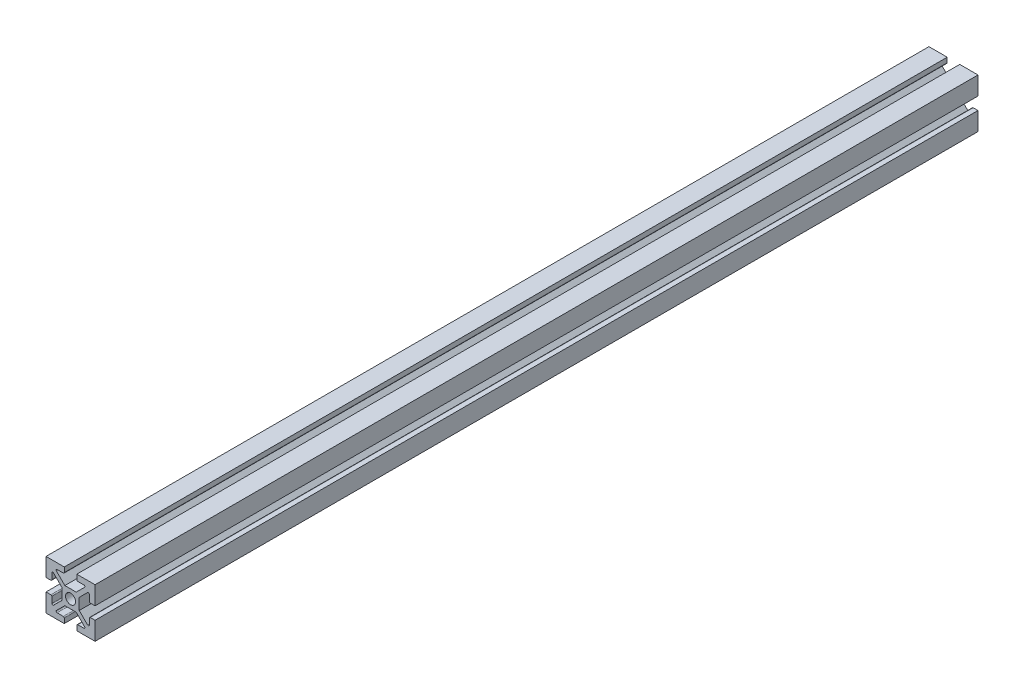
SolidWorks part; units mm, degrees
ref_plane "Front Plane" through (0, 0, 0) normal (0, 0, 1) x (1, 0, 0)
ref_plane "Top Plane" through (0, 0, 0) normal (0, 1, 0) x (1, 0, 0)
ref_plane "Right Plane" through (0, 0, 0) normal (1, 0, 0) x (0, 0, -1)
sketch "Sketch2" plane through (0, 0, 0) normal (0, 0, 1) x (1, 0, 0)
  line L1 (-12.7, -12.7) -> (12.7, -12.7)
  line L2 (-12.7, -12.7) -> (-12.7, 12.7)
  line L3 (-12.7, 12.7) -> (12.7, 12.7)
  line L4 (12.7, -12.7) -> (12.7, 12.7)
  line L5 (-12.7, -12.7) -> (12.7, 12.7) construction
  line L6 (-12.7, 12.7) -> (12.7, -12.7) construction
  point P0 (0, 0)
  dimension "D1" = 25.4
  dimension "D2" = 25.4
extrude "Boss-Extrude2" add sketch "Sketch2" along normal blind 457.2
sketch "Sketch3" plane through (0, 0, 457.2) normal (0, 0, 1) x (1, 0, 0)
  line L0 (-3.2385, 12.7) -> (-3.2385, 10.2185)
  line L1 (12.7, 12.7) -> (-12.7, 12.7) construction
  line L2 (-3.7465, 9.7105) -> (-6.9215, 9.7105)
  line L3 (-7.2807, 8.8433) -> (-2.9459, 4.5085)
  line L4 (-2.9459, 4.5085) -> (2.9459, 4.5085)
  line L5 (-3.2385, 12.7) -> (3.2385, 12.7)
  line L6 (0, -1000) -> (0, 49000) construction
  line L7 (7.2807, 8.8433) -> (2.9459, 4.5085)
  line L8 (3.7465, 9.7105) -> (6.9215, 9.7105)
  line L9 (3.2385, 12.7) -> (3.2385, 10.2185)
  line L10 (12.7, 3.2385) -> (10.2185, 3.2385)
  line L11 (9.7105, 3.7465) -> (9.7105, 6.9215)
  line L12 (8.8433, 7.2807) -> (4.5085, 2.9459)
  line L13 (4.5085, 2.9459) -> (4.5085, -2.9459)
  line L14 (12.7, 3.2385) -> (12.7, -3.2385)
  line L15 (8.8433, -7.2807) -> (4.5085, -2.9459)
  line L16 (9.7105, -3.7465) -> (9.7105, -6.9215)
  line L17 (12.7, -3.2385) -> (10.2185, -3.2385)
  line L18 (3.2385, -12.7) -> (3.2385, -10.2185)
  line L19 (3.7465, -9.7105) -> (6.9215, -9.7105)
  line L20 (7.2807, -8.8433) -> (2.9459, -4.5085)
  line L21 (2.9459, -4.5085) -> (-2.9459, -4.5085)
  line L22 (3.2385, -12.7) -> (-3.2385, -12.7)
  line L23 (-7.2807, -8.8433) -> (-2.9459, -4.5085)
  line L24 (-3.7465, -9.7105) -> (-6.9215, -9.7105)
  line L25 (-3.2385, -12.7) -> (-3.2385, -10.2185)
  line L26 (-12.7, -3.2385) -> (-10.2185, -3.2385)
  line L27 (-9.7105, -3.7465) -> (-9.7105, -6.9215)
  line L28 (-8.8433, -7.2807) -> (-4.5085, -2.9459)
  line L29 (-4.5085, -2.9459) -> (-4.5085, 2.9459)
  line L30 (-12.7, -3.2385) -> (-12.7, 3.2385)
  line L31 (-8.8433, 7.2807) -> (-4.5085, 2.9459)
  line L32 (-9.7105, 3.7465) -> (-9.7105, 6.9215)
  line L33 (-12.7, 3.2385) -> (-10.2185, 3.2385)
  line L34 (-12.7, 12.7) -> (-12.7, -12.7) construction
  line L35 (12.7, -12.7) -> (12.7, 12.7) construction
  circle A0 centre (0, 0) radius 2.6035
  arc A1 (-6.9215, 9.7105) -> (-7.2807, 8.8433) centre (-6.9215, 9.2025) ccw
  arc A2 (9.7105, 6.9215) -> (8.8433, 7.2807) centre (9.2025, 6.9215) ccw
  arc A3 (8.8433, -7.2807) -> (9.7105, -6.9215) centre (9.2025, -6.9215) ccw
  arc A4 (7.2807, 8.8433) -> (6.9215, 9.7105) centre (6.9215, 9.2025) ccw
  arc A5 (3.7465, 9.7105) -> (3.2385, 10.2185) centre (3.7465, 10.2185) cw
  arc A6 (-3.2385, 10.2185) -> (-3.7465, 9.7105) centre (-3.7465, 10.2185) cw
  arc A7 (9.7105, -3.7465) -> (10.2185, -3.2385) centre (10.2185, -3.7465) cw
  arc A8 (10.2185, 3.2385) -> (9.7105, 3.7465) centre (10.2185, 3.7465) cw
  arc A9 (6.9215, -9.7105) -> (7.2807, -8.8433) centre (6.9215, -9.2025) ccw
  arc A10 (-7.2807, -8.8433) -> (-6.9215, -9.7105) centre (-6.9215, -9.2025) ccw
  arc A11 (-3.7465, -9.7105) -> (-3.2385, -10.2185) centre (-3.7465, -10.2185) cw
  arc A12 (3.2385, -10.2185) -> (3.7465, -9.7105) centre (3.7465, -10.2185) cw
  arc A13 (-9.7105, -6.9215) -> (-8.8433, -7.2807) centre (-9.2025, -6.9215) ccw
  arc A14 (-8.8433, 7.2807) -> (-9.7105, 6.9215) centre (-9.2025, 6.9215) ccw
  arc A15 (-9.7105, 3.7465) -> (-10.2185, 3.2385) centre (-10.2185, 3.7465) cw
  arc A16 (-10.2185, -3.2385) -> (-9.7105, -3.7465) centre (-10.2185, -3.7465) cw
  point P12 (0, 12.7)
  point P13 (0, 4.5085)
  point P19 (-8.1479, 9.7105)
  point P20 (2.9459, 4.5085)
  point P22 (-2.9459, 4.5085)
  point P25 (2.9459, 4.5085)
  point P28 (8.1479, 9.7105)
  point P31 (3.2385, 9.7105)
  point P34 (-3.2385, 9.7105)
  point P36 (-2.9459, 4.5085)
  point P42 (12.7, 0)
  point P43 (4.5085, 0)
  point P60 (0, -12.7)
  point P61 (0, -4.5085)
  point P78 (-12.7, 0)
  point P79 (-4.5085, 0)
  dimension "D2" = 5.207
  dimension "D3" = 0.508
  dimension "D5" = 4
  dimension "D7" = 13.843
  dimension "D1" = 6.477
  dimension "D4" = 9.017
  dimension "D6" = 2.2098
extrude "Cut-Extrude2" cut sketch "Sketch3" against normal through all
